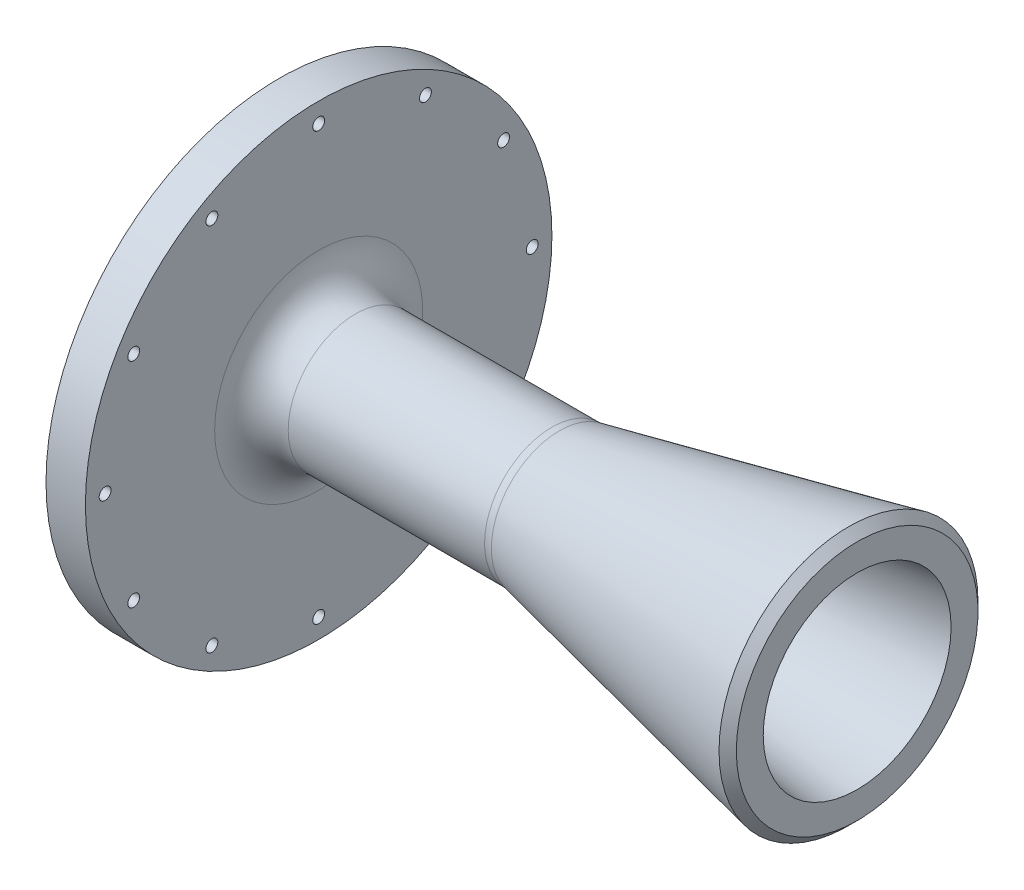
SolidWorks part; units mm, degrees
material "Stainless Steel (ferritic)"
ref_plane "Front Plane" through (0, 0, 0) normal (0, 0, 1) x (1, 0, 0)
ref_plane "Top Plane" through (0, 0, 0) normal (0, 1, 0) x (1, 0, 0)
ref_plane "Right Plane" through (0, 0, 0) normal (1, 0, 0) x (0, 0, -1)
sketch "Sketch2" plane through (0, 0, 0) normal (0, 0, 1) x (1, 0, 0)
  line L0 (0, 0) -> (165.0115, 0) construction
  line L1 (0, 20.5835) -> (0, 56.388)
  line L2 (0, 56.388) -> (9.525, 56.388)
  line L3 (9.525, 56.388) -> (9.525, 16.256)
  line L11 (66.8065, 16.256) -> (139.7, 31.75)
  line L17 (139.7, 31.75) -> (139.7, 22.7076)
  line L18 (60.325, 12.7208) -> (60.325, 14.351)
  line L19 (60.325, 14.351) -> (10.795, 14.351)
  line L20 (0, 20.5835) -> (10.795, 14.351)
  line L21 (60.325, 12.7208) -> (139.7, 22.7076)
  line L22 (9.525, 16.256) -> (66.8065, 16.256)
  dimension "D2" = 9.525
  dimension "D3" = 1.905
  dimension "D4" = 10.795
  dimension "D5" = 14.351
  dimension "D6" = 31.75
  dimension "D7" = 7.171
  dimension "D8" = 139.7
  dimension "D9" = 22.7076
  dimension "D10" = 30
  dimension "D11" = 56.388
  dimension "D12" = 49.53
  dimension "D13" = 12
revolve "Main Structure" add sketch "Sketch2" angle 360 about L0
sketch "Sketch4" plane through (0, 0, 0) normal (-1, 0, 0) x (0, 0, 1)
  circle A0 centre (0, 0) radius 51.6255 construction
  circle A1 centre (0, -51.6255) radius 2.146
  circle A2 centre (-25.8127, -44.709) radius 2.146
  circle A3 centre (-44.709, -25.8128) radius 2.146
  circle A4 centre (-51.6255, 0) radius 2.146
  circle A5 centre (-44.709, 25.8127) radius 2.146
  circle A6 centre (-25.8128, 44.709) radius 2.146
  circle A7 centre (0, 51.6255) radius 2.146
  circle A8 centre (25.8127, 44.709) radius 2.146
  circle A9 centre (44.709, 25.8128) radius 2.146
  circle A10 centre (51.6255, 0) radius 2.146
  circle A11 centre (44.709, -25.8127) radius 2.146
  circle A12 centre (25.8128, -44.709) radius 2.146
  point P29 (0, 0)
  dimension "D1" = 12
  dimension "D2" = 103.251
hole_wizard "Flange Holes" positions "Sketch7" profile "Sketch8" hole size "#33" standard "ANSI Inch" end condition up to next
sketch "Sketch7" plane through (0, 0, 0) normal (-1, 0, 0) x (0, 0, 1)
  point P0 (0, -51.6255)
  point P3 (-25.8127, -44.709)
  point P6 (-44.709, -25.8128)
  point P9 (-51.6255, 0)
  point P12 (-44.709, 25.8127)
  point P15 (-25.8128, 44.709)
  point P18 (0, 51.6255)
  point P21 (25.8127, 44.709)
  point P24 (44.709, 25.8128)
  point P27 (51.6255, 0)
  point P30 (44.709, -25.8127)
  point P33 (25.8128, -44.709)
sketch "Sketch8" plane through (0, -51.6255, 0) normal (0, 1, 0) x (0, 0, 1)
  line L0 (0, 0) -> (0, 9.525)
  line L1 (0, 9.525) -> (1.4351, 9.525)
  line L2 (1.4351, 9.525) -> (1.4351, 0)
  line L5 (1.4351, 0) -> (0, 0)
  line L11 (0, -6.35) -> (0, 107.95) construction
  dimension "Thru Hole Dia." = 2.8702
  dimension "Thru Hole Depth" = 9.525
sketch "Sketch9" plane through (0, 0, 0) normal (-1, 0, 0) x (0, 0, 1)
  line L0 (0, 0) -> (-67.6727, 18.1329) construction
  line L1 (0, 0) -> (-51.6255, 0) construction
  circle A0 centre (0, 0) radius 51.6255 construction
  circle A1 centre (-49.8664, 13.3617) radius 2.9451
  circle A2 centre (49.8664, -13.3617) radius 2.9451
  point P14 (0, 0)
  dimension "D1" = 15
  dimension "D2" = 2
hole_wizard "Dowel Holes" positions "Sketch10" profile "Sketch11" hole size "3/16" standard "ANSI Inch"
sketch "Sketch10" plane through (0, 0, 0) normal (-1, 0, 0) x (0, 0, 1)
  point P0 (49.8664, -13.3617)
  point P3 (-49.8664, 13.3617)
sketch "Sketch11" plane through (0, -13.3617, 49.8664) normal (0, 1, 0) x (0, 0, 1)
  line L0 (0, 0) -> (0, 7.7808)
  line L1 (0, 7.7808) -> (2.3812, 6.35)
  line L2 (2.3812, 6.35) -> (2.3812, 0)
  line L5 (2.3812, 0) -> (0, 0)
  line L10 (0, 7.7808) -> (-2.3812, 6.35) construction
  line L11 (0, -6.35) -> (0, 107.95) construction
  dimension "Hole Dia." = 4.7625
  dimension "Hole Depth" = 6.35
  dimension "Drill Angle" = 118
fillet "Fillet1" radius 8.89 2 edges at (66.8065, 0, 16.256) (9.525, 0, 16.256)
sketch "Sketch13" plane through (0, 0, 0) normal (0, 1, 0) x (1, 0, 0)
  line L0 (0, 38.1) -> (3.3333, 0)
  line L1 (0, 56.388) -> (0, -56.388) construction
  line L2 (3.3333, 0) -> (0, 0)
  line L3 (0, 0) -> (0, 38.1)
  dimension "D1" = 38.1
  dimension "D2" = 5
revolve "Cut-Revolve1" cut sketch "Sketch13" angle 360 about L2
chamfer "Chamfer1" distance 2.54 angle 45 1 edges at (139.7, 0, 31.75)
